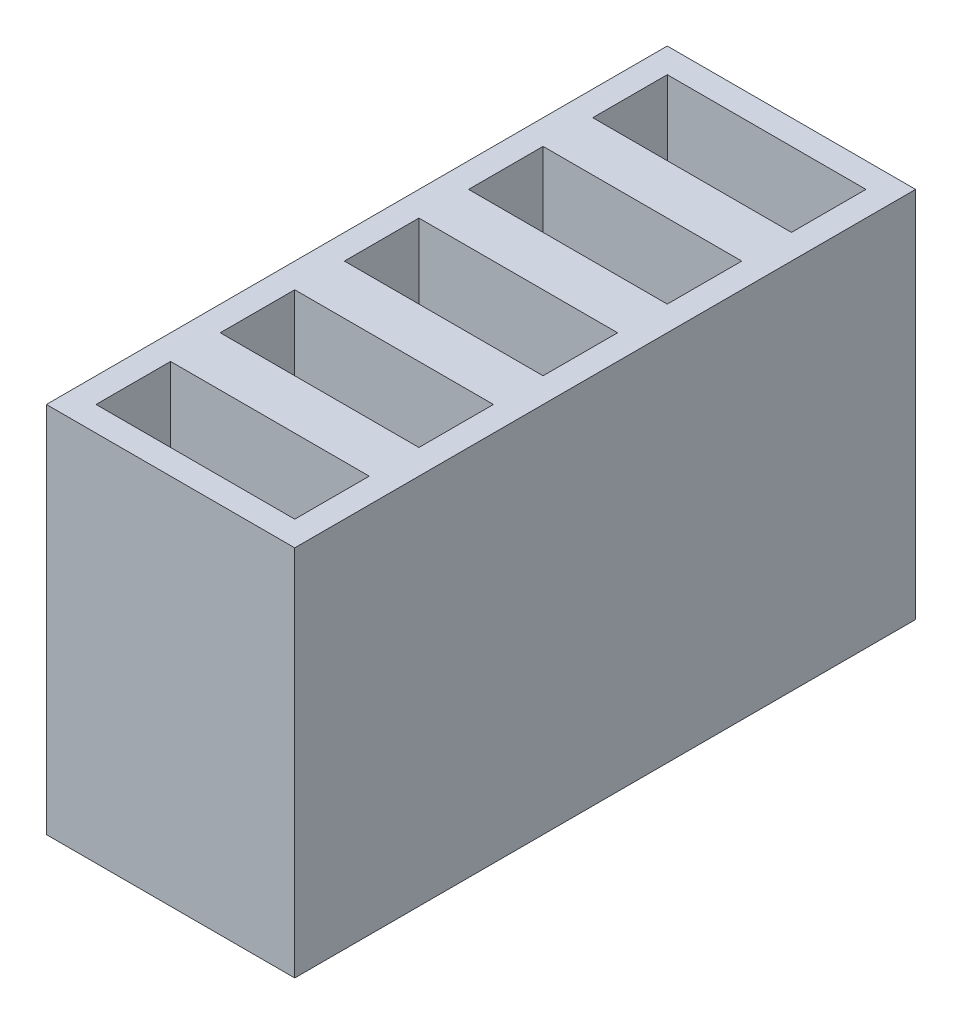
SolidWorks part; units mm, degrees
ref_plane "Alzado" through (0, 0, 0) normal (0, 0, 1) x (1, 0, 0)
ref_plane "Planta" through (0, 0, 0) normal (0, 1, 0) x (1, 0, 0)
ref_plane "Vista lateral" through (0, 0, 0) normal (1, 0, 0) x (0, 0, -1)
sketch "Croquis1" plane through (0, 0, 0) normal (0, 1, 0) x (1, 0, 0)
  line L1 (-47.21, 19.1168) -> (-27.21, 19.1168)
  line L2 (-47.21, 19.1168) -> (-47.21, -30.8832)
  line L3 (-47.21, -30.8832) -> (-27.21, -30.8832)
  line L4 (-27.21, 19.1168) -> (-27.21, -30.8832)
  dimension "D1" = 20
  dimension "D2" = 50
extrude "Saliente-Extruir1" add sketch "Croquis1" along normal blind 30
sketch "Croquis2" plane through (0, 30, 0) normal (0, 1, 0) x (1, 0, 0)
  line L0 (-37.21, 19.1168) -> (-37.21, -30.8832) construction
  line L1 (-27.21, 19.1168) -> (-47.21, 19.1168) construction
  line L2 (-47.21, -30.8832) -> (-27.21, -30.8832) construction
  line L3 (-29.21, -22.8832) -> (-29.21, -28.8832)
  line L4 (-45.21, 1.1168) -> (-45.21, 7.1168)
  line L6 (-45.21, -18.8832) -> (-45.21, -12.8832)
  line L8 (-45.21, -8.8832) -> (-45.21, -2.8832)
  line L9 (-29.21, -12.8832) -> (-29.21, -18.8832)
  line L11 (-29.21, -2.8832) -> (-29.21, -8.8832)
  line L17 (-45.21, 7.1168) -> (-29.21, 7.1168)
  line L18 (-45.21, -2.8832) -> (-29.21, -2.8832)
  line L19 (-45.21, -12.8832) -> (-29.21, -12.8832)
  line L20 (-45.21, -22.8832) -> (-29.21, -22.8832)
  line L21 (-45.21, 17.1168) -> (-29.21, 17.1168)
  line L22 (-29.21, 17.1168) -> (-29.21, 11.1168)
  line L23 (-45.21, -28.8832) -> (-29.21, -28.8832)
  line L24 (-45.21, -28.8832) -> (-45.21, -22.8832)
  line L25 (-45.21, 11.1168) -> (-29.21, 11.1168)
  line L26 (-45.21, 1.1168) -> (-29.21, 1.1168)
  line L27 (-45.21, -8.8832) -> (-29.21, -8.8832)
  line L28 (-45.21, -18.8832) -> (-29.21, -18.8832)
  line L40 (-45.21, 11.1168) -> (-45.21, 17.1168)
  line L42 (-29.21, 7.1168) -> (-29.21, 1.1168)
extrude "Cortar-Extruir1" cut sketch "Croquis2" against normal offset from surface (25 mm away) 5 up to face at (-37.21, 0, 5.8832)
